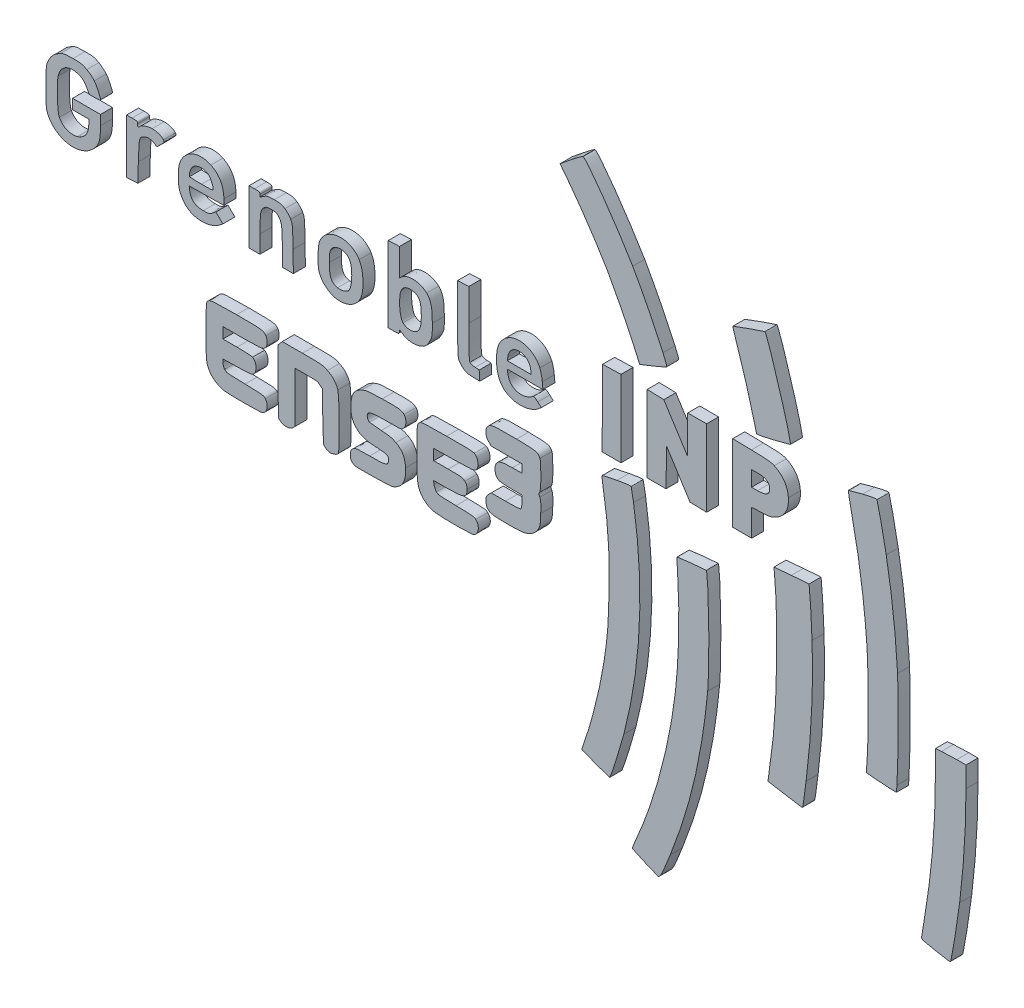
SolidWorks part; units mm, degrees
ref_plane "Plan de face" through (0, 0, 0) normal (0, 0, 1) x (1, 0, 0)
ref_plane "Plan de dessus" through (0, 0, 0) normal (0, 1, 0) x (1, 0, 0)
ref_plane "Plan de droite" through (0, 0, 0) normal (1, 0, 0) x (0, 0, -1)
sketch "Model" plane through (0, 0, 0) normal (0, 0, 1) x (1, 0, 0)
  line L0 (370.4983, 93.602) -> (370.5001, 103.7665)
  line L1 (370.5001, 103.7665) -> (373.0314, 104.0056)
  line L2 (379.4064, 104.2473) -> (383.25, 104.25)
  line L3 (383.25, 104.25) -> (383.25, 95.68)
  line L4 (303.5095, 133.3398) -> (303.2851, 135.617)
  line L5 (303.2851, 135.617) -> (310.5175, 136.2461)
  line L6 (354.5099, 82.5938) -> (354.2904, 79.875)
  line L7 (354.2904, 79.875) -> (351.9889, 79.9271)
  line L8 (81.7747, 107.625) -> (73.875, 107.625)
  line L9 (73.875, 107.625) -> (73.875, 105.375)
  line L10 (73.875, 105.375) -> (73.875, 103.125)
  line L11 (73.875, 103.125) -> (79.7122, 103.125)
  line L12 (79.8364, 96.0608) -> (73.875, 95.9341)
  line L13 (73.875, 95.9341) -> (73.875, 94.6961)
  line L14 (115.4135, 96.5017) -> (115.3125, 105.816)
  line L15 (115.3125, 105.816) -> (114.2603, 106.7205)
  line L16 (108.5416, 107.625) -> (103.875, 107.625)
  line L17 (103.875, 107.625) -> (103.875, 97.108)
  line L18 (103.875, 97.108) -> (103.875, 86.5909)
  line L19 (103.875, 86.5909) -> (102.9545, 85.6705)
  line L20 (97.8228, 85.4665) -> (96.9375, 86.183)
  line L21 (96.9375, 86.183) -> (96.83, 99.3047)
  line L22 (96.83, 99.3047) -> (96.7226, 112.4263)
  line L23 (96.7226, 112.4263) -> (97.6419, 113.4944)
  line L24 (97.6419, 113.4944) -> (98.5613, 114.5625)
  line L25 (98.5613, 114.5625) -> (106.9369, 114.5625)
  line L26 (170.0499, 107.6988) -> (161.625, 107.5851)
  line L27 (161.625, 107.5851) -> (161.625, 105.3551)
  line L28 (161.625, 105.3551) -> (161.625, 103.125)
  line L29 (161.625, 103.125) -> (167.642, 103.125)
  line L30 (166.7347, 96) -> (161.5269, 96)
  line L31 (161.5269, 96) -> (161.7514, 94.6162)
  line L32 (184.4712, 102.4038) -> (185.5673, 103.5)
  line L33 (185.5673, 103.5) -> (191.5212, 103.5)
  line L34 (198.375, 106.7625) -> (198.375, 109.125)
  line L35 (198.375, 109.125) -> (194.0801, 109.125)
  line L36 (194.4004, 117) -> (198.375, 117)
  line L37 (198.375, 117) -> (198.375, 118.6875)
  line L38 (198.375, 118.6875) -> (198.375, 120.375)
  line L39 (198.375, 120.375) -> (191.9712, 120.375)
  line L40 (191.9712, 120.375) -> (185.5673, 120.375)
  line L41 (185.5673, 120.375) -> (184.4712, 121.4712)
  line L42 (20.5312, 163.5011) -> (18.1875, 163.5022)
  line L43 (18.1875, 163.5022) -> (17.25, 165.2558)
  line L44 (18, 152.613) -> (18, 154.5)
  line L45 (18, 154.5) -> (14.625, 154.5)
  line L46 (14.625, 154.5) -> (11.25, 154.5)
  line L47 (11.25, 154.5) -> (11.25, 156.5625)
  line L48 (11.25, 156.5625) -> (11.25, 158.625)
  line L49 (11.25, 158.625) -> (17.0625, 158.625)
  line L50 (17.0625, 158.625) -> (22.875, 158.625)
  line L51 (22.875, 158.625) -> (22.875, 154.5681)
  line L52 (74.25, 153.8788) -> (74.25, 151.5162)
  line L53 (74.25, 151.5162) -> (67.0313, 151.4143)
  line L54 (67.0313, 151.4143) -> (59.8125, 151.3125)
  line L55 (59.8125, 151.3125) -> (59.9398, 150.1875)
  line L56 (69.5307, 146.3878) -> (70.9406, 147.4632)
  line L57 (70.9406, 147.4632) -> (72.3884, 146.0495)
  line L58 (72.3884, 146.0495) -> (73.8361, 144.6357)
  line L59 (73.8361, 144.6357) -> (72.306, 143.4249)
  line L60 (148.4879, 142.5086) -> (147.4288, 143.2627)
  line L61 (147.4288, 143.2627) -> (147.3082, 142.4126)
  line L62 (144.9375, 141.5625) -> (142.6875, 141.5625)
  line L63 (142.6875, 141.5625) -> (142.6875, 157.3125)
  line L64 (142.6875, 157.3125) -> (142.6875, 173.0625)
  line L65 (142.6875, 173.0625) -> (145.0312, 173.1741)
  line L66 (145.0312, 173.1741) -> (147.375, 173.2858)
  line L67 (147.375, 173.2858) -> (147.375, 167.5775)
  line L68 (147.375, 167.5775) -> (147.375, 161.8693)
  line L69 (147.375, 161.8693) -> (148.2188, 162.6597)
  line L70 (206.8299, 154.2188) -> (207.0969, 151.5)
  line L71 (207.0969, 151.5) -> (199.6866, 151.5)
  line L72 (199.6866, 151.5) -> (192.2762, 151.5)
  line L73 (192.2762, 151.5) -> (192.4857, 149.9387)
  line L74 (204.9375, 146.0026) -> (206.4375, 144.6871)
  line L75 (206.4375, 144.6871) -> (205.3125, 143.747)
  line L76 (192.4857, 156.0613) -> (192.2762, 154.5)
  line L77 (192.2762, 154.5) -> (197.25, 154.5)
  line L78 (197.25, 154.5) -> (202.2238, 154.5)
  line L79 (202.2238, 154.5) -> (202.0143, 156.0613)
  line L80 (33.75, 152.6071) -> (33.75, 163.875)
  line L81 (33.75, 163.875) -> (36, 163.875)
  line L82 (48.0151, 160.3279) -> (46.409, 158.6914)
  line L83 (46.409, 158.6914) -> (45.2357, 159.4068)
  line L84 (38.625, 149.4375) -> (38.4375, 141.5625)
  line L85 (38.4375, 141.5625) -> (36.0938, 141.4509)
  line L86 (36.0938, 141.4509) -> (33.75, 141.3392)
  line L87 (33.75, 141.3392) -> (33.75, 152.6071)
  line L88 (84.75, 152.625) -> (84.75, 163.875)
  line L89 (84.75, 163.875) -> (87, 163.875)
  line L90 (89.25, 162.9322) -> (89.25, 161.9894)
  line L91 (89.25, 161.9894) -> (90.8161, 163.0259)
  line L92 (103.0562, 150.0938) -> (103.1749, 141.375)
  line L93 (103.1749, 141.375) -> (100.8999, 141.375)
  line L94 (100.8999, 141.375) -> (98.625, 141.375)
  line L95 (98.625, 141.375) -> (98.6087, 148.0312)
  line L96 (89.25, 148.6995) -> (89.25, 141.375)
  line L97 (89.25, 141.375) -> (87, 141.375)
  line L98 (87, 141.375) -> (84.75, 141.375)
  line L99 (84.75, 141.375) -> (84.75, 152.625)
  line L100 (171.5625, 159.375) -> (171.5625, 173.0625)
  line L101 (171.5625, 173.0625) -> (173.9063, 173.1741)
  line L102 (173.9063, 173.1741) -> (176.25, 173.2858)
  line L103 (176.25, 173.2858) -> (176.25, 160.0271)
  line L104 (178.875, 145.4238) -> (180.5625, 145.3125)
  line L105 (180.5625, 145.3125) -> (180.6758, 143.3438)
  line L106 (180.6758, 143.3438) -> (180.7892, 141.375)
  line L107 (180.7892, 141.375) -> (178.6133, 141.4185)
  line L108 (231.8397, 157.2188) -> (231.9375, 173.0625)
  line L109 (231.9375, 173.0625) -> (235.7813, 173.1694)
  line L110 (235.7813, 173.1694) -> (239.625, 173.2762)
  line L111 (239.625, 173.2762) -> (239.625, 157.3256)
  line L112 (239.625, 157.3256) -> (239.625, 141.375)
  line L113 (239.625, 141.375) -> (235.6834, 141.375)
  line L114 (235.6834, 141.375) -> (231.7419, 141.375)
  line L115 (231.7419, 141.375) -> (231.8397, 157.2188)
  line L116 (250.5, 157.3266) -> (250.5, 173.2781)
  line L117 (250.5, 173.2781) -> (253.9678, 173.1703)
  line L118 (253.9678, 173.1703) -> (257.4355, 173.0625)
  line L119 (257.4355, 173.0625) -> (262.3115, 165.4141)
  line L120 (262.3115, 165.4141) -> (267.1875, 157.7657)
  line L121 (267.1875, 157.7657) -> (267.2889, 165.5079)
  line L122 (267.2889, 165.5079) -> (267.3902, 173.25)
  line L123 (267.3902, 173.25) -> (271.3201, 173.25)
  line L124 (271.3201, 173.25) -> (275.25, 173.25)
  line L125 (275.25, 173.25) -> (275.25, 157.2984)
  line L126 (275.25, 157.2984) -> (275.25, 141.3469)
  line L127 (275.25, 141.3469) -> (271.7923, 141.4547)
  line L128 (271.7923, 141.4547) -> (268.3347, 141.5625)
  line L129 (268.3347, 141.5625) -> (263.4486, 149.2383)
  line L130 (263.4486, 149.2383) -> (258.5625, 156.9141)
  line L131 (258.5625, 156.9141) -> (258.4611, 149.1445)
  line L132 (258.4611, 149.1445) -> (258.3598, 141.375)
  line L133 (258.3598, 141.375) -> (254.4299, 141.375)
  line L134 (254.4299, 141.375) -> (250.5, 141.375)
  line L135 (250.5, 141.375) -> (250.5, 157.3266)
  line L136 (286.125, 157.3504) -> (286.125, 173.3258)
  line L137 (286.125, 173.3258) -> (293.9062, 173.168)
  line L138 (297.8485, 152.6824) -> (294, 152.5399)
  line L139 (294, 152.5399) -> (294, 146.9575)
  line L140 (294, 146.9575) -> (294, 141.375)
  line L141 (294, 141.375) -> (290.0625, 141.375)
  line L142 (290.0625, 141.375) -> (286.125, 141.375)
  line L143 (286.125, 141.375) -> (286.125, 157.3504)
  line L144 (296.4622, 166.125) -> (294, 166.125)
  line L145 (294, 166.125) -> (294, 162.9375)
  line L146 (294, 162.9375) -> (294, 159.75)
  line L147 (294, 159.75) -> (296.4561, 159.75)
  line L148 (218.1652, 231.4251) -> (214.2237, 236.5378)
  line L149 (214.2237, 236.5378) -> (218.7289, 240.1947)
  spline S0 degree 3 poles (249.5625, 2.2496) (246.8813, 3.4795) (244.553, 4.5338) (244.3887, 4.5925) knots 0 0 0 0 1 1 1 1
  spline S1 degree 3 poles (244.3887, 4.5925) (244.2244, 4.6512) (244.8458, 6.404) (245.7697, 8.4878) knots 0 0 0 0 1 1 1 1
  spline S2 degree 3 poles (245.7697, 8.4878) (253.7191, 26.4169) (259.9566, 49.7657) (262.286, 70.3125) knots 0 0 0 0 1 1 1 1
  spline S3 degree 3 poles (262.286, 70.3125) (263.7235, 82.9917) (264.0926, 99.8702) (263.2108, 112.5965) knots 0 0 0 0 1 1 1 1
  spline S4 degree 3 poles (263.2108, 112.5965) (262.9706, 116.0629) (262.8546, 118.9796) (262.953, 119.078) knots 0 0 0 0 1 1 1 1
  spline S5 degree 3 poles (262.953, 119.078) (263.1965, 119.3215) (274.8687, 120.5063) (275.0674, 120.3076) knots 0 0 0 0 1 1 1 1
  spline S6 degree 3 poles (275.0674, 120.3076) (276.1342, 119.2408) (276.6184, 86.4395) (275.7057, 77.0625) knots 0 0 0 0 1 1 1 1
  spline S7 degree 3 poles (275.7057, 77.0625) (273.2513, 51.8443) (268.5915, 31.8716) (260.1262, 10.2858) knots 0 0 0 0 1 1 1 1
  spline S8 degree 3 poles (260.1262, 10.2858) (256.9535, 2.1957) (255.8814, -0.001) (255.1094, 0.0067) knots 0 0 0 0 1 1 1 1
  spline S9 degree 3 poles (255.1094, 0.0067) (254.7399, 0.0105) (252.2437, 1.0197) (249.5625, 2.2496) knots 0 0 0 0 1 1 1 1
  spline S10 degree 3 poles (228.9375, 27.634) (225.8438, 28.7843) (223.2808, 29.7485) (223.2421, 29.7768) knots 0 0 0 0 1 1 1 1
  spline S11 degree 3 poles (223.2421, 29.7768) (223.2034, 29.8051) (223.6806, 31.2591) (224.3025, 33.0079) knots 0 0 0 0 1 1 1 1
  spline S12 degree 3 poles (224.3025, 33.0079) (227.4977, 41.9923) (230.9762, 55.967) (232.5126, 65.9913) knots 0 0 0 0 1 1 1 1
  spline S13 degree 3 poles (232.5126, 65.9913) (234.0491, 76.0162) (234.4431, 80.9083) (234.6425, 92.4409) knots 0 0 0 0 1 1 1 1
  spline S14 degree 3 poles (234.6425, 92.4409) (234.8945, 107.0164) (234.225, 116.8141) (232.1485, 128.9391) knots 0 0 0 0 1 1 1 1
  spline S15 degree 3 poles (232.1485, 128.9391) (231.6792, 131.6792) (231.606, 132.8621) (231.8986, 132.9744) knots 0 0 0 0 1 1 1 1
  spline S16 degree 3 poles (231.8986, 132.9744) (232.1262, 133.0617) (234.8438, 133.6195) (237.9375, 134.214) knots 0 0 0 0 1 1 1 1
  spline S17 degree 3 poles (237.9375, 134.214) (241.627, 134.923) (243.6451, 135.1627) (243.8027, 134.9106) knots 0 0 0 0 1 1 1 1
  spline S18 degree 3 poles (243.8027, 134.9106) (243.9348, 134.6992) (244.394, 132.3125) (244.8232, 129.6069) knots 0 0 0 0 1 1 1 1
  spline S19 degree 3 poles (244.8232, 129.6069) (249.396, 100.7826) (248.031, 71.8998) (240.7826, 44.1054) knots 0 0 0 0 1 1 1 1
  spline S20 degree 3 poles (240.7826, 44.1054) (239.0568, 37.4879) (235.2125, 25.4904) (234.8277, 25.5213) knots 0 0 0 0 1 1 1 1
  spline S21 degree 3 poles (234.8277, 25.5213) (234.6818, 25.533) (232.0313, 26.4837) (228.9375, 27.634) knots 0 0 0 0 1 1 1 1
  spline S22 degree 3 poles (370.6875, 30.9249) (365.3011, 31.969) (364.694, 32.1634) (364.7511, 32.8252) knots 0 0 0 0 1 1 1 1
  spline S23 degree 3 poles (364.7511, 32.8252) (364.7861, 33.2307) (365.3292, 36.6) (365.9579, 40.3125) knots 0 0 0 0 1 1 1 1
  spline S24 degree 3 poles (365.9579, 40.3125) (369.0163, 58.3714) (370.4952, 75.7294) (370.4983, 93.602) knots 0 0 0 0 1 1 1 1
  spline S25 degree 3 poles (373.0314, 104.0056) (374.4236, 104.1371) (377.2923, 104.2459) (379.4064, 104.2473) knots 0 0 0 0 1 1 1 1
  spline S26 degree 3 poles (383.25, 95.68) (383.25, 81.8276) (382.3466, 67.311) (380.6094, 53.25) knots 0 0 0 0 1 1 1 1
  spline S27 degree 3 poles (380.6094, 53.25) (379.7864, 46.5878) (377.3549, 31.4444) (376.9404, 30.3996) knots 0 0 0 0 1 1 1 1
  spline S28 degree 3 poles (376.9404, 30.3996) (376.7072, 29.8115) (376.2201, 29.8524) (370.6875, 30.9249) knots 0 0 0 0 1 1 1 1
  spline S29 degree 3 poles (307.6875, 55.9592) (303.975, 56.5743) (300.8915, 57.1202) (300.8353, 57.1723) knots 0 0 0 0 1 1 1 1
  spline S30 degree 3 poles (300.8353, 57.1723) (300.779, 57.2244) (300.9834, 58.9366) (301.2894, 60.9772) knots 0 0 0 0 1 1 1 1
  spline S31 degree 3 poles (301.2894, 60.9772) (303.4274, 75.2359) (304.1691, 85.0917) (304.3934, 102.2242) knots 0 0 0 0 1 1 1 1
  spline S32 degree 3 poles (304.3934, 102.2242) (304.5718, 115.8529) (304.304, 125.2808) (303.5095, 133.3398) knots 0 0 0 0 1 1 1 1
  spline S33 degree 3 poles (310.5175, 136.2461) (314.4953, 136.5921) (317.7959, 136.8291) (317.8521, 136.7729) knots 0 0 0 0 1 1 1 1
  spline S34 degree 3 poles (317.8521, 136.7729) (318.1289, 136.4961) (318.7847, 126.5555) (319.1526, 117.0609) knots 0 0 0 0 1 1 1 1
  spline S35 degree 3 poles (319.1526, 117.0609) (319.7845, 100.7548) (318.901, 82.2522) (316.6698, 65.0625) knots 0 0 0 0 1 1 1 1
  spline S36 degree 3 poles (316.6698, 65.0625) (315.3559, 54.9399) (315.3215, 54.7451) (314.8569, 54.7954) knots 0 0 0 0 1 1 1 1
  spline S37 degree 3 poles (314.8569, 54.7954) (314.6262, 54.8204) (311.4, 55.344) (307.6875, 55.9592) knots 0 0 0 0 1 1 1 1
  spline S38 degree 3 poles (345.7642, 80.3191) (343.6064, 80.5061) (341.7987, 80.7013) (341.747, 80.753) knots 0 0 0 0 1 1 1 1
  spline S39 degree 3 poles (341.747, 80.753) (341.6954, 80.8046) (341.8427, 82.9485) (342.0743, 85.5172) knots 0 0 0 0 1 1 1 1
  spline S40 degree 3 poles (342.0743, 85.5172) (342.6552, 91.9587) (342.6463, 118.3501) (342.0607, 126) knots 0 0 0 0 1 1 1 1
  spline S41 degree 3 poles (342.0607, 126) (340.7379, 143.2796) (338.8816, 156.2244) (335.4, 172.4479) knots 0 0 0 0 1 1 1 1
  spline S42 degree 3 poles (335.4, 172.4479) (334.6758, 175.8224) (334.1711, 178.6711) (334.2783, 178.7783) knots 0 0 0 0 1 1 1 1
  spline S43 degree 3 poles (334.2783, 178.7783) (334.3855, 178.8855) (337.0526, 179.6088) (340.2053, 180.3857) knots 0 0 0 0 1 1 1 1
  spline S44 degree 3 poles (340.2053, 180.3857) (344.3498, 181.407) (346.0068, 181.6776) (346.1878, 181.3627) knots 0 0 0 0 1 1 1 1
  spline S45 degree 3 poles (346.1878, 181.3627) (346.5109, 180.8005) (348.8175, 170.0514) (350.0427, 163.3982) knots 0 0 0 0 1 1 1 1
  spline S46 degree 3 poles (350.0427, 163.3982) (352.2836, 151.2299) (353.9911, 136.6709) (354.7809, 123) knots 0 0 0 0 1 1 1 1
  spline S47 degree 3 poles (354.7809, 123) (355.2111, 115.5532) (355.0335, 89.0793) (354.5099, 82.5938) knots 0 0 0 0 1 1 1 1
  spline S48 degree 3 poles (351.9889, 79.9271) (350.7231, 79.9557) (347.922, 80.1321) (345.7642, 80.3191) knots 0 0 0 0 1 1 1 1
  spline S49 degree 3 poles (74.3789, 84.7516) (70.5248, 85.5486) (67.9098, 88.004) (67.152, 91.5374) knots 0 0 0 0 1 1 1 1
  spline S50 degree 3 poles (67.152, 91.5374) (66.606, 94.0831) (66.6179, 111.7998) (67.1664, 113.0035) knots 0 0 0 0 1 1 1 1
  spline S51 degree 3 poles (67.1664, 113.0035) (67.9041, 114.6226) (68.8068, 114.75) (79.5423, 114.75) knots 0 0 0 0 1 1 1 1
  spline S52 degree 3 poles (79.5423, 114.75) (89.8381, 114.75) (90.7243, 114.6436) (91.7693, 113.2825) knots 0 0 0 0 1 1 1 1
  spline S53 degree 3 poles (91.7693, 113.2825) (92.3593, 112.5141) (92.3593, 109.8609) (91.7693, 109.0925) knots 0 0 0 0 1 1 1 1
  spline S54 degree 3 poles (91.7693, 109.0925) (90.7539, 107.7699) (89.7667, 107.625) (81.7747, 107.625) knots 0 0 0 0 1 1 1 1
  spline S55 degree 3 poles (79.7122, 103.125) (82.9226, 103.125) (85.8526, 102.9627) (86.2232, 102.7643) knots 0 0 0 0 1 1 1 1
  spline S56 degree 3 poles (86.2232, 102.7643) (87.9155, 101.8587) (88.1312, 98.3013) (86.5791, 96.8952) knots 0 0 0 0 1 1 1 1
  spline S57 degree 3 poles (86.5791, 96.8952) (85.8966, 96.277) (85.0442, 96.1715) (79.8364, 96.0608) knots 0 0 0 0 1 1 1 1
  spline S58 degree 3 poles (73.875, 94.6961) (73.875, 94.0152) (74.1973, 93.0597) (74.5913, 92.5728) knots 0 0 0 0 1 1 1 1
  spline S59 degree 3 poles (74.5913, 92.5728) (75.2925, 91.7062) (75.4716, 91.6835) (83.063, 91.5) knots 0 0 0 0 1 1 1 1
  spline S60 degree 3 poles (83.063, 91.5) (90.6546, 91.3165) (90.8334, 91.2938) (91.5342, 90.4272) knots 0 0 0 0 1 1 1 1
  spline S61 degree 3 poles (91.5342, 90.4272) (92.6248, 89.0784) (92.5001, 86.6159) (91.2831, 85.4716) knots 0 0 0 0 1 1 1 1
  spline S62 degree 3 poles (91.2831, 85.4716) (90.335, 84.5802) (90.1765, 84.5612) (83.1269, 84.4959) knots 0 0 0 0 1 1 1 1
  spline S63 degree 3 poles (83.1269, 84.4959) (79.1727, 84.4593) (75.2361, 84.5743) (74.3789, 84.7516) knots 0 0 0 0 1 1 1 1
  spline S64 degree 3 poles (117.1068, 84.9286) (116.3899, 85.2403) (115.8228, 85.8044) (115.7079, 86.3202) knots 0 0 0 0 1 1 1 1
  spline S65 degree 3 poles (115.7079, 86.3202) (115.6015, 86.7972) (115.4691, 91.3789) (115.4135, 96.5017) knots 0 0 0 0 1 1 1 1
  spline S66 degree 3 poles (114.2603, 106.7205) (113.2702, 107.5717) (112.9331, 107.625) (108.5416, 107.625) knots 0 0 0 0 1 1 1 1
  spline S67 degree 3 poles (102.9545, 85.6705) (101.7785, 84.4944) (99.1528, 84.39) (97.8228, 85.4665) knots 0 0 0 0 1 1 1 1
  spline S68 degree 3 poles (106.9369, 114.5625) (115.2933, 114.5625) (115.3173, 114.5603) (117.3902, 113.5421) knots 0 0 0 0 1 1 1 1
  spline S69 degree 3 poles (117.3902, 113.5421) (119.6543, 112.4301) (120.8717, 111.0621) (121.7091, 108.6889) knots 0 0 0 0 1 1 1 1
  spline S70 degree 3 poles (121.7091, 108.6889) (122.3654, 106.8286) (122.5054, 87.0528) (121.8706, 85.8668) knots 0 0 0 0 1 1 1 1
  spline S71 degree 3 poles (121.8706, 85.8668) (121.6619, 85.4768) (120.8603, 84.9826) (120.0893, 84.7685) knots 0 0 0 0 1 1 1 1
  spline S72 degree 3 poles (120.0893, 84.7685) (118.3933, 84.2975) (118.5815, 84.2874) (117.1068, 84.9286) knots 0 0 0 0 1 1 1 1
  spline S73 degree 3 poles (162.3386, 84.7548) (160.2283, 85.1118) (158.7548, 85.8474) (157.3636, 87.2386) knots 0 0 0 0 1 1 1 1
  spline S74 degree 3 poles (157.3636, 87.2386) (154.8527, 89.7496) (154.4227, 92.3259) (154.5727, 103.9591) knots 0 0 0 0 1 1 1 1
  spline S75 degree 3 poles (154.5727, 103.9591) (154.6847, 112.6409) (154.7081, 112.8762) (155.5411, 113.7091) knots 0 0 0 0 1 1 1 1
  spline S76 degree 3 poles (155.5411, 113.7091) (156.3839, 114.5517) (156.5292, 114.5637) (166.9786, 114.6596) knots 0 0 0 0 1 1 1 1
  spline S77 degree 3 poles (166.9786, 114.6596) (175.022, 114.7334) (177.7875, 114.6411) (178.5, 114.2748) knots 0 0 0 0 1 1 1 1
  spline S78 degree 3 poles (178.5, 114.2748) (179.6781, 113.6693) (180.3923, 111.6178) (179.9553, 110.0943) knots 0 0 0 0 1 1 1 1
  spline S79 degree 3 poles (179.9553, 110.0943) (179.3078, 107.8363) (179.2527, 107.823) (170.0499, 107.6988) knots 0 0 0 0 1 1 1 1
  spline S80 degree 3 poles (167.642, 103.125) (173.5305, 103.125) (173.6788, 103.1053) (174.5795, 102.2045) knots 0 0 0 0 1 1 1 1
  spline S81 degree 3 poles (174.5795, 102.2045) (175.2769, 101.5072) (175.4971, 100.8936) (175.4881, 99.6733) knots 0 0 0 0 1 1 1 1
  spline S82 degree 3 poles (175.4881, 99.6733) (175.4647, 96.5098) (174.2498, 96) (166.7347, 96) knots 0 0 0 0 1 1 1 1
  spline S83 degree 3 poles (161.7514, 94.6162) (161.8749, 93.8551) (162.3232, 92.8847) (162.7475, 92.4599) knots 0 0 0 0 1 1 1 1
  spline S84 degree 3 poles (162.7475, 92.4599) (163.4656, 91.7411) (164.032, 91.6794) (170.9158, 91.5707) knots 0 0 0 0 1 1 1 1
  spline S85 degree 3 poles (170.9158, 91.5707) (177.7167, 91.4634) (178.3771, 91.3933) (179.1146, 90.7007) knots 0 0 0 0 1 1 1 1
  spline S86 degree 3 poles (179.1146, 90.7007) (180.9303, 88.9957) (180.3485, 85.5813) (178.1094, 84.8007) knots 0 0 0 0 1 1 1 1
  spline S87 degree 3 poles (178.1094, 84.8007) (176.731, 84.3202) (165.1079, 84.2864) (162.3386, 84.7548) knots 0 0 0 0 1 1 1 1
  spline S88 degree 3 poles (127.8553, 85.4407) (127.101, 86.0517) (126.9442, 86.5021) (126.975, 87.9693) knots 0 0 0 0 1 1 1 1
  spline S89 degree 3 poles (126.975, 87.9693) (127.0054, 89.4186) (127.2034, 89.9186) (128.0272, 90.6272) knots 0 0 0 0 1 1 1 1
  spline S90 degree 3 poles (128.0272, 90.6272) (128.9955, 91.4602) (129.3105, 91.5003) (134.9272, 91.5055) knots 0 0 0 0 1 1 1 1
  spline S91 degree 3 poles (134.9272, 91.5055) (141.6264, 91.5118) (142.6213, 91.7787) (142.8015, 93.6178) knots 0 0 0 0 1 1 1 1
  spline S92 degree 3 poles (142.8015, 93.6178) (142.9887, 95.528) (142.2882, 95.8683) (137.7224, 96.0847) knots 0 0 0 0 1 1 1 1
  spline S93 degree 3 poles (137.7224, 96.0847) (132.9709, 96.3099) (130.9524, 97.021) (129.1107, 99.1187) knots 0 0 0 0 1 1 1 1
  spline S94 degree 3 poles (129.1107, 99.1187) (127.5039, 100.9488) (127.0133, 102.7897) (127.1765, 106.3767) knots 0 0 0 0 1 1 1 1
  spline S95 degree 3 poles (127.1765, 106.3767) (127.3554, 110.3095) (128.455, 112.1119) (131.5586, 113.5596) knots 0 0 0 0 1 1 1 1
  spline S96 degree 3 poles (131.5586, 113.5596) (133.5539, 114.4903) (134.0944, 114.5612) (140.1694, 114.6887) knots 0 0 0 0 1 1 1 1
  spline S97 degree 3 poles (140.1694, 114.6887) (147.2237, 114.8367) (148.1473, 114.7277) (149.2595, 113.6155) knots 0 0 0 0 1 1 1 1
  spline S98 degree 3 poles (149.2595, 113.6155) (150.3779, 112.4971) (150.2802, 109.7462) (149.0795, 108.5455) knots 0 0 0 0 1 1 1 1
  spline S99 degree 3 poles (149.0795, 108.5455) (148.179, 107.6449) (148.0294, 107.625) (142.1597, 107.625) knots 0 0 0 0 1 1 1 1
  spline S100 degree 3 poles (142.1597, 107.625) (135.9274, 107.625) (134.4485, 107.3413) (134.0444, 106.0681) knots 0 0 0 0 1 1 1 1
  spline S101 degree 3 poles (134.0444, 106.0681) (133.7419, 105.115) (134.1495, 103.9994) (134.9205, 103.67) knots 0 0 0 0 1 1 1 1
  spline S102 degree 3 poles (134.9205, 103.67) (135.2736, 103.5191) (137.4453, 103.2695) (139.7464, 103.1152) knots 0 0 0 0 1 1 1 1
  spline S103 degree 3 poles (139.7464, 103.1152) (143.3092, 102.8764) (144.2181, 102.6781) (145.8682, 101.78) knots 0 0 0 0 1 1 1 1
  spline S104 degree 3 poles (145.8682, 101.78) (148.5365, 100.3277) (149.6851, 98.3192) (149.9174, 94.6992) knots 0 0 0 0 1 1 1 1
  spline S105 degree 3 poles (149.9174, 94.6992) (150.1975, 90.3347) (148.8415, 87.4252) (145.7595, 85.7778) knots 0 0 0 0 1 1 1 1
  spline S106 degree 3 poles (145.7595, 85.7778) (144.3035, 84.9995) (143.6186, 84.9286) (136.4803, 84.8174) knots 0 0 0 0 1 1 1 1
  spline S107 degree 3 poles (136.4803, 84.8174) (129.2556, 84.7048) (128.7157, 84.7439) (127.8553, 85.4407) knots 0 0 0 0 1 1 1 1
  spline S108 degree 3 poles (185.3733, 96.1717) (183.8985, 96.8132) (183.375, 97.7517) (183.375, 99.7542) knots 0 0 0 0 1 1 1 1
  spline S109 degree 3 poles (183.375, 99.7542) (183.375, 100.9712) (183.6124, 101.5451) (184.4712, 102.4038) knots 0 0 0 0 1 1 1 1
  spline S110 degree 3 poles (191.5212, 103.5) (195.6519, 103.5) (197.6128, 103.6378) (197.925, 103.95) knots 0 0 0 0 1 1 1 1
  spline S111 degree 3 poles (197.925, 103.95) (198.1798, 104.2048) (198.375, 105.425) (198.375, 106.7625) knots 0 0 0 0 1 1 1 1
  spline S112 degree 3 poles (194.0801, 109.125) (191.718, 109.125) (189.3741, 109.3124) (188.8715, 109.5414) knots 0 0 0 0 1 1 1 1
  spline S113 degree 3 poles (188.8715, 109.5414) (187.2692, 110.2714) (186.6284, 112.8747) (187.552, 114.9018) knots 0 0 0 0 1 1 1 1
  spline S114 degree 3 poles (187.552, 114.9018) (188.2703, 116.4785) (189.9726, 117) (194.4004, 117) knots 0 0 0 0 1 1 1 1
  spline S115 degree 3 poles (184.4712, 121.4712) (183.008, 122.9343) (182.9087, 125.5677) (184.2654, 126.9245) knots 0 0 0 0 1 1 1 1
  spline S116 degree 3 poles (184.2654, 126.9245) (185.4904, 128.1495) (187.1675, 128.3277) (196.1262, 128.185) knots 0 0 0 0 1 1 1 1
  spline S117 degree 3 poles (196.1262, 128.185) (204.3311, 128.0542) (205.0241, 127.9054) (205.8483, 126.0963) knots 0 0 0 0 1 1 1 1
  spline S118 degree 3 poles (205.8483, 126.0963) (206.4592, 124.7555) (206.3741, 114.6881) (205.7446, 113.8272) knots 0 0 0 0 1 1 1 1
  spline S119 degree 3 poles (205.7446, 113.8272) (205.3187, 113.2447) (205.3256, 112.9631) (205.7888, 112.0346) knots 0 0 0 0 1 1 1 1
  spline S120 degree 3 poles (205.7888, 112.0346) (206.2101, 111.1901) (206.3029, 109.8689) (206.1865, 106.3728) knots 0 0 0 0 1 1 1 1
  spline S121 degree 3 poles (206.1865, 106.3728) (206.0541, 102.397) (205.9163, 101.5984) (205.1111, 100.1416) knots 0 0 0 0 1 1 1 1
  spline S122 degree 3 poles (205.1111, 100.1416) (203.934, 98.0123) (201.7385, 96.4833) (199.1676, 96.0027) knots 0 0 0 0 1 1 1 1
  spline S123 degree 3 poles (199.1676, 96.0027) (196.1107, 95.4311) (186.8138, 95.545) (185.3733, 96.1717) knots 0 0 0 0 1 1 1 1
  spline S124 degree 3 poles (9.1002, 141.3767) (5.47, 142.136) (2.4536, 144.4224) (1.0844, 147.4524) knots 0 0 0 0 1 1 1 1
  spline S125 degree 3 poles (1.0844, 147.4524) (0.23, 149.3434) (0.1875, 149.8107) (0.1875, 157.3125) knots 0 0 0 0 1 1 1 1
  spline S126 degree 3 poles (0.1875, 157.3125) (0.1875, 165.1791) (0.1886, 165.1898) (1.2379, 167.3265) knots 0 0 0 0 1 1 1 1
  spline S127 degree 3 poles (1.2379, 167.3265) (2.3573, 169.606) (3.6558, 170.9057) (6.1438, 172.2367) knots 0 0 0 0 1 1 1 1
  spline S128 degree 3 poles (6.1438, 172.2367) (7.4395, 172.9298) (8.29, 173.0625) (11.4375, 173.0625) knots 0 0 0 0 1 1 1 1
  spline S129 degree 3 poles (11.4375, 173.0625) (14.8884, 173.0625) (15.3467, 172.9743) (17.1838, 171.9566) knots 0 0 0 0 1 1 1 1
  spline S130 degree 3 poles (17.1838, 171.9566) (18.2818, 171.3484) (19.6921, 170.2044) (20.3178, 169.4144) knots 0 0 0 0 1 1 1 1
  spline S131 degree 3 poles (20.3178, 169.4144) (21.3466, 168.1155) (22.875, 164.8022) (22.875, 163.871) knots 0 0 0 0 1 1 1 1
  spline S132 degree 3 poles (22.875, 163.871) (22.875, 163.6658) (21.8275, 163.5005) (20.5312, 163.5011) knots 0 0 0 0 1 1 1 1
  spline S133 degree 3 poles (17.25, 165.2558) (16.1291, 167.3524) (14.9273, 168.3026) (12.7885, 168.7831) knots 0 0 0 0 1 1 1 1
  spline S134 degree 3 poles (12.7885, 168.7831) (9.1506, 169.6005) (6.0431, 167.508) (5.2547, 163.71) knots 0 0 0 0 1 1 1 1
  spline S135 degree 3 poles (5.2547, 163.71) (4.5797, 160.4588) (4.8931, 150.5586) (5.7199, 149.0135) knots 0 0 0 0 1 1 1 1
  spline S136 degree 3 poles (5.7199, 149.0135) (7.1993, 146.2484) (10.1992, 145.0034) (13.2941, 145.8699) knots 0 0 0 0 1 1 1 1
  spline S137 degree 3 poles (13.2941, 145.8699) (16.3053, 146.7129) (18, 149.1413) (18, 152.613) knots 0 0 0 0 1 1 1 1
  spline S138 degree 3 poles (22.875, 154.5681) (22.875, 149.0487) (22.2594, 147.0855) (19.7383, 144.5643) knots 0 0 0 0 1 1 1 1
  spline S139 degree 3 poles (19.7383, 144.5643) (16.9865, 141.8126) (12.8877, 140.5844) (9.1002, 141.3767) knots 0 0 0 0 1 1 1 1
  spline S140 degree 3 poles (62.6941, 141.3831) (59.6696, 142.0114) (57.5741, 143.7618) (56.1883, 146.8172) knots 0 0 0 0 1 1 1 1
  spline S141 degree 3 poles (56.1883, 146.8172) (55.4787, 148.3817) (55.3407, 149.3313) (55.3439, 152.625) knots 0 0 0 0 1 1 1 1
  spline S142 degree 3 poles (55.3439, 152.625) (55.3473, 155.9221) (55.4891, 156.8813) (56.2164, 158.5227) knots 0 0 0 0 1 1 1 1
  spline S143 degree 3 poles (56.2164, 158.5227) (58.4381, 163.5364) (63.9339, 165.6413) (68.8391, 163.3572) knots 0 0 0 0 1 1 1 1
  spline S144 degree 3 poles (68.8391, 163.3572) (72.3174, 161.7376) (74.25, 158.3521) (74.25, 153.8788) knots 0 0 0 0 1 1 1 1
  spline S145 degree 3 poles (59.9398, 150.1875) (60.3203, 146.8261) (62.0781, 145.3284) (65.6542, 145.319) knots 0 0 0 0 1 1 1 1
  spline S146 degree 3 poles (65.6542, 145.319) (67.7973, 145.3133) (68.3058, 145.4535) (69.5307, 146.3878) knots 0 0 0 0 1 1 1 1
  spline S147 degree 3 poles (72.306, 143.4249) (69.9324, 141.5466) (65.9642, 140.7037) (62.6941, 141.3831) knots 0 0 0 0 1 1 1 1
  spline S148 degree 3 poles (69.75, 155.2424) (69.75, 156.5205) (68.5989, 158.9308) (67.7105, 159.5129) knots 0 0 0 0 1 1 1 1
  spline S149 degree 3 poles (67.7105, 159.5129) (65.511, 160.9541) (62.2229, 160.452) (60.9291, 158.4773) knots 0 0 0 0 1 1 1 1
  spline S150 degree 3 poles (60.9291, 158.4773) (60.2344, 157.417) (59.5949, 155.0301) (59.9187, 154.7063) knots 0 0 0 0 1 1 1 1
  spline S151 degree 3 poles (59.9187, 154.7063) (60.0322, 154.5928) (62.2906, 154.5) (64.9375, 154.5) knots 0 0 0 0 1 1 1 1
  spline S152 degree 3 poles (64.9375, 154.5) (69.4836, 154.5) (69.75, 154.5411) (69.75, 155.2424) knots 0 0 0 0 1 1 1 1
  spline S153 degree 3 poles (120.744, 141.3409) (117.46, 141.9948) (114.3959, 144.9393) (113.7256, 148.0852) knots 0 0 0 0 1 1 1 1
  spline S154 degree 3 poles (113.7256, 148.0852) (113.2621, 150.2606) (113.3938, 156.0372) (113.9506, 157.9531) knots 0 0 0 0 1 1 1 1
  spline S155 degree 3 poles (113.9506, 157.9531) (116.0459, 165.1632) (126.6175, 166.5379) (130.5768, 160.1151) knots 0 0 0 0 1 1 1 1
  spline S156 degree 3 poles (130.5768, 160.1151) (132.5537, 156.9081) (132.751, 149.5365) (130.9534, 146.0402) knots 0 0 0 0 1 1 1 1
  spline S157 degree 3 poles (130.9534, 146.0402) (129.1099, 142.4546) (124.8947, 140.5143) (120.744, 141.3409) knots 0 0 0 0 1 1 1 1
  spline S158 degree 3 poles (125.5276, 146.1979) (126.7767, 146.8663) (127.5, 149.2994) (127.5, 152.8321) knots 0 0 0 0 1 1 1 1
  spline S159 degree 3 poles (127.5, 152.8321) (127.5, 157.6184) (126.3723, 159.6205) (123.4563, 160.0117) knots 0 0 0 0 1 1 1 1
  spline S160 degree 3 poles (123.4563, 160.0117) (121.4663, 160.2786) (119.4821, 159.309) (118.7165, 157.6956) knots 0 0 0 0 1 1 1 1
  spline S161 degree 3 poles (118.7165, 157.6956) (118.3051, 156.8286) (118.125, 155.3497) (118.125, 152.8375) knots 0 0 0 0 1 1 1 1
  spline S162 degree 3 poles (118.125, 152.8375) (118.125, 147.7897) (118.9308, 146.0904) (121.5961, 145.5181) knots 0 0 0 0 1 1 1 1
  spline S163 degree 3 poles (121.5961, 145.5181) (122.8442, 145.2501) (124.1922, 145.4832) (125.5276, 146.1979) knots 0 0 0 0 1 1 1 1
  spline S164 degree 3 poles (150.9922, 141.4009) (150.1973, 141.5954) (149.0704, 142.0938) (148.4879, 142.5086) knots 0 0 0 0 1 1 1 1
  spline S165 degree 3 poles (147.3082, 142.4126) (147.1981, 141.637) (146.9903, 141.5625) (144.9375, 141.5625) knots 0 0 0 0 1 1 1 1
  spline S166 degree 3 poles (148.2188, 162.6597) (150.7448, 165.0259) (155.9475, 164.7518) (158.7087, 162.1071) knots 0 0 0 0 1 1 1 1
  spline S167 degree 3 poles (158.7087, 162.1071) (160.4559, 160.4336) (161.0625, 157.9414) (161.0625, 152.4375) knots 0 0 0 0 1 1 1 1
  spline S168 degree 3 poles (161.0625, 152.4375) (161.0625, 147.7708) (161.0144, 147.4663) (159.9375, 145.3125) knots 0 0 0 0 1 1 1 1
  spline S169 degree 3 poles (159.9375, 145.3125) (159.0875, 143.6126) (158.4458, 142.8638) (157.3125, 142.2499) knots 0 0 0 0 1 1 1 1
  spline S170 degree 3 poles (157.3125, 142.2499) (155.496, 141.2658) (152.9452, 140.9232) (150.9922, 141.4009) knots 0 0 0 0 1 1 1 1
  spline S171 degree 3 poles (154.7704, 146.3555) (155.9794, 147.4512) (156.45, 149.2602) (156.45, 152.8125) knots 0 0 0 0 1 1 1 1
  spline S172 degree 3 poles (156.45, 152.8125) (156.45, 157.8711) (155.5231, 159.6338) (152.6612, 160.0177) knots 0 0 0 0 1 1 1 1
  spline S173 degree 3 poles (152.6612, 160.0177) (150.6681, 160.285) (148.9915, 159.5605) (148.2315, 158.1034) knots 0 0 0 0 1 1 1 1
  spline S174 degree 3 poles (148.2315, 158.1034) (146.8783, 155.509) (147.2851, 147.8764) (148.8521, 146.4582) knots 0 0 0 0 1 1 1 1
  spline S175 degree 3 poles (148.8521, 146.4582) (150.4218, 145.0376) (153.2618, 144.9883) (154.7704, 146.3555) knots 0 0 0 0 1 1 1 1
  spline S176 degree 3 poles (195.4752, 141.3881) (190.2019, 142.4532) (187.7662, 146.0664) (187.7636, 152.8276) knots 0 0 0 0 1 1 1 1
  spline S177 degree 3 poles (187.7636, 152.8276) (187.7621, 156.9429) (188.6259, 159.4137) (190.8353, 161.6135) knots 0 0 0 0 1 1 1 1
  spline S178 degree 3 poles (190.8353, 161.6135) (195.438, 166.1963) (203.2457, 164.6602) (205.8208, 158.6653) knots 0 0 0 0 1 1 1 1
  spline S179 degree 3 poles (205.8208, 158.6653) (206.229, 157.715) (206.6831, 155.7141) (206.8299, 154.2188) knots 0 0 0 0 1 1 1 1
  spline S180 degree 3 poles (192.4857, 149.9387) (193.1108, 145.2777) (198.3775, 143.6437) (202.6875, 146.7735) knots 0 0 0 0 1 1 1 1
  spline S181 degree 3 poles (202.6875, 146.7735) (203.3735, 147.2716) (203.5656, 147.2058) (204.9375, 146.0026) knots 0 0 0 0 1 1 1 1
  spline S182 degree 3 poles (205.3125, 143.747) (202.8306, 141.673) (198.8228, 140.7119) (195.4752, 141.3881) knots 0 0 0 0 1 1 1 1
  spline S183 degree 3 poles (202.0143, 156.0613) (201.7355, 158.1403) (200.7042, 159.4443) (198.8098, 160.1134) knots 0 0 0 0 1 1 1 1
  spline S184 degree 3 poles (198.8098, 160.1134) (195.807, 161.174) (192.9236, 159.3265) (192.4857, 156.0613) knots 0 0 0 0 1 1 1 1
  spline S185 degree 3 poles (36, 163.875) (38.15, 163.875) (38.25, 163.8333) (38.25, 162.9375) knots 0 0 0 0 1 1 1 1
  spline S186 degree 3 poles (38.25, 162.9375) (38.25, 161.9681) (38.7633, 161.6886) (39.2116, 162.414) knots 0 0 0 0 1 1 1 1
  spline S187 degree 3 poles (39.2116, 162.414) (39.705, 163.2123) (42.5796, 164.2336) (44.3558, 164.2418) knots 0 0 0 0 1 1 1 1
  spline S188 degree 3 poles (44.3558, 164.2418) (46.342, 164.2509) (48.2818, 163.5796) (49.0919, 162.6028) knots 0 0 0 0 1 1 1 1
  spline S189 degree 3 poles (49.0919, 162.6028) (49.5633, 162.0345) (49.4452, 161.7851) (48.0151, 160.3279) knots 0 0 0 0 1 1 1 1
  spline S190 degree 3 poles (45.2357, 159.4068) (43.8208, 160.2696) (42.3418, 160.321) (40.8675, 159.5586) knots 0 0 0 0 1 1 1 1
  spline S191 degree 3 poles (40.8675, 159.5586) (38.9704, 158.5776) (38.8272, 157.9315) (38.625, 149.4375) knots 0 0 0 0 1 1 1 1
  spline S192 degree 3 poles (87, 163.875) (89.1534, 163.875) (89.25, 163.8345) (89.25, 162.9322) knots 0 0 0 0 1 1 1 1
  spline S193 degree 3 poles (90.8161, 163.0259) (92.1834, 163.931) (92.7457, 164.0625) (95.2481, 164.0625) knots 0 0 0 0 1 1 1 1
  spline S194 degree 3 poles (95.2481, 164.0625) (97.7468, 164.0625) (98.3142, 163.9303) (99.6747, 163.0308) knots 0 0 0 0 1 1 1 1
  spline S195 degree 3 poles (99.6747, 163.0308) (100.5336, 162.463) (101.6178, 161.2828) (102.0863, 160.4058) knots 0 0 0 0 1 1 1 1
  spline S196 degree 3 poles (102.0863, 160.4058) (102.8893, 158.9028) (102.9442, 158.3184) (103.0562, 150.0938) knots 0 0 0 0 1 1 1 1
  spline S197 degree 3 poles (98.6087, 148.0312) (98.5896, 155.8251) (98.3239, 157.5965) (96.9715, 158.9489) knots 0 0 0 0 1 1 1 1
  spline S198 degree 3 poles (96.9715, 158.9489) (96.1488, 159.7717) (95.645, 159.9375) (93.9684, 159.9375) knots 0 0 0 0 1 1 1 1
  spline S199 degree 3 poles (93.9684, 159.9375) (92.4841, 159.9375) (91.7323, 159.7401) (91.1126, 159.1875) knots 0 0 0 0 1 1 1 1
  spline S200 degree 3 poles (91.1126, 159.1875) (89.4689, 157.7219) (89.25, 156.4893) (89.25, 148.6995) knots 0 0 0 0 1 1 1 1
  spline S201 degree 3 poles (175.6875, 141.6498) (174.4587, 141.9575) (172.9073, 143.2293) (172.2131, 144.4983) knots 0 0 0 0 1 1 1 1
  spline S202 degree 3 poles (172.2131, 144.4983) (171.6292, 145.5655) (171.5625, 147.0916) (171.5625, 159.375) knots 0 0 0 0 1 1 1 1
  spline S203 degree 3 poles (176.25, 160.0271) (176.25, 149.9989) (176.3642, 146.6181) (176.7188, 146.1518) knots 0 0 0 0 1 1 1 1
  spline S204 degree 3 poles (176.7188, 146.1518) (177.0018, 145.7795) (177.8562, 145.4911) (178.875, 145.4238) knots 0 0 0 0 1 1 1 1
  spline S205 degree 3 poles (178.6133, 141.4185) (177.4166, 141.4424) (176.1, 141.5465) (175.6875, 141.6498) knots 0 0 0 0 1 1 1 1
  spline S206 degree 3 poles (293.9062, 173.168) (300.7934, 173.0284) (301.887, 172.9201) (303.4235, 172.2253) knots 0 0 0 0 1 1 1 1
  spline S207 degree 3 poles (303.4235, 172.2253) (306.9408, 170.635) (309.036, 167.5664) (309.3029, 163.6146) knots 0 0 0 0 1 1 1 1
  spline S208 degree 3 poles (309.3029, 163.6146) (309.5968, 159.2615) (307.6067, 155.7162) (303.8327, 153.8698) knots 0 0 0 0 1 1 1 1
  spline S209 degree 3 poles (303.8327, 153.8698) (302.0151, 152.9805) (301.1235, 152.8036) (297.8485, 152.6824) knots 0 0 0 0 1 1 1 1
  spline S210 degree 3 poles (299.9732, 160.2986) (301.1459, 160.9051) (301.506, 161.5618) (301.4881, 163.0619) knots 0 0 0 0 1 1 1 1
  spline S211 degree 3 poles (301.4881, 163.0619) (301.463, 165.168) (299.8927, 166.125) (296.4622, 166.125) knots 0 0 0 0 1 1 1 1
  spline S212 degree 3 poles (296.4561, 159.75) (297.8783, 159.75) (299.3589, 159.981) (299.9732, 160.2986) knots 0 0 0 0 1 1 1 1
  spline S213 degree 3 poles (296.0528, 180.142) (295.9776, 180.3733) (295.3053, 182.925) (294.5588, 185.8125) knots 0 0 0 0 1 1 1 1
  spline S214 degree 3 poles (294.5588, 185.8125) (292.6826, 193.069) (290.9588, 198.8845) (288.3013, 206.9229) knots 0 0 0 0 1 1 1 1
  spline S215 degree 3 poles (288.3013, 206.9229) (287.0538, 210.696) (286.096, 213.839) (286.1729, 213.9073) knots 0 0 0 0 1 1 1 1
  spline S216 degree 3 poles (286.1729, 213.9073) (286.4511, 214.1544) (299.0808, 218.625) (299.5008, 218.625) knots 0 0 0 0 1 1 1 1
  spline S217 degree 3 poles (299.5008, 218.625) (300.5399, 218.625) (310.8848, 184.0098) (310.0849, 183.2099) knots 0 0 0 0 1 1 1 1
  spline S218 degree 3 poles (310.0849, 183.2099) (309.984, 183.109) (306.8163, 182.2829) (303.0455, 181.374) knots 0 0 0 0 1 1 1 1
  spline S219 degree 3 poles (303.0455, 181.374) (298.4391, 180.2638) (296.1446, 179.8595) (296.0528, 180.142) knots 0 0 0 0 1 1 1 1
  spline S220 degree 3 poles (245.8396, 184.2188) (243.7643, 189.207) (237.1967, 202.2742) (234.0127, 207.75) knots 0 0 0 0 1 1 1 1
  spline S221 degree 3 poles (234.0127, 207.75) (230.0565, 214.554) (222.7056, 225.5357) (218.1652, 231.4251) knots 0 0 0 0 1 1 1 1
  spline S222 degree 3 poles (218.7289, 240.1947) (221.2068, 242.2059) (223.4899, 243.8709) (223.8025, 243.8945) knots 0 0 0 0 1 1 1 1
  spline S223 degree 3 poles (223.8025, 243.8945) (225.0922, 243.9921) (238.0358, 225.7053) (244.4756, 214.6875) knots 0 0 0 0 1 1 1 1
  spline S224 degree 3 poles (244.4756, 214.6875) (248.0351, 208.5975) (254.4485, 195.9488) (257.0839, 189.821) knots 0 0 0 0 1 1 1 1
  spline S225 degree 3 poles (257.0839, 189.821) (258.6108, 186.2707) (258.8188, 185.5232) (258.3603, 185.2342) knots 0 0 0 0 1 1 1 1
  spline S226 degree 3 poles (258.3603, 185.2342) (257.8717, 184.9262) (247.6547, 180.75) (247.3898, 180.75) knots 0 0 0 0 1 1 1 1
  spline S227 degree 3 poles (247.3898, 180.75) (247.3309, 180.75) (246.6333, 182.3109) (245.8396, 184.2188) knots 0 0 0 0 1 1 1 1
extrude "Boss.-Extru.1" add sketch "Model" along normal blind 5
